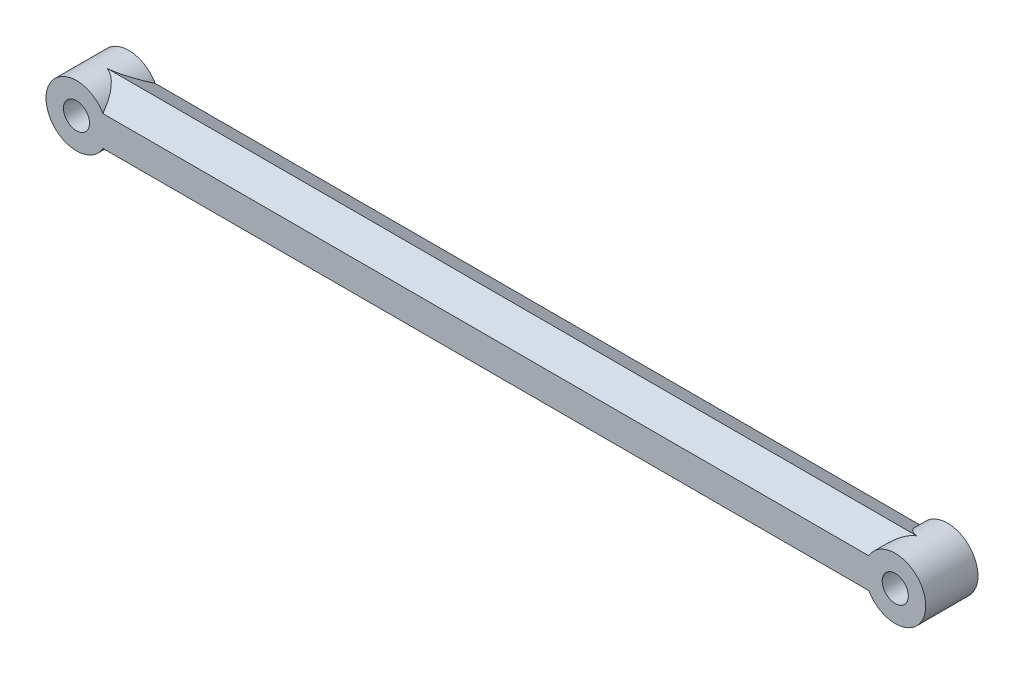
SolidWorks part; units mm, degrees
ref_plane "Front Plane" through (0, 0, 0) normal (0, 0, 1) x (1, 0, 0)
ref_plane "Top Plane" through (0, 0, 0) normal (0, 1, 0) x (1, 0, 0)
ref_plane "Right Plane" through (0, 0, 0) normal (1, 0, 0) x (0, 0, -1)
sketch "Sketch1" plane through (0, 0, 0) normal (0, 0, 1) x (1, 0, 0)
  line L0 (-47, 0) -> (47, 0) construction
  circle A0 centre (-47, 0) radius 1.5
  circle A1 centre (47, 0) radius 1.5
  circle A6 centre (-47, 0) radius 3.5
  circle A7 centre (47, 0) radius 3.5
  dimension "D2" = 3
  dimension "D3" = 7
  dimension "D1" = 94
extrude "Boss-Extrude1" add sketch "Sketch1" along normal mid plane 6
sketch "Sketch2" plane through (0, 0, 0) normal (1, 0, 0) x (0, 0, -1)
  line L0 (0, 0) -> (0, 3.4641) construction
  line L1 (-3, 1.7321) -> (-3, -1.7321)
  line L2 (-3, -1.7321) -> (0, -3.4641)
  line L3 (0, -3.4641) -> (3, -1.7321)
  line L4 (3, -1.7321) -> (3, 1.7321)
  line L5 (3, 1.7321) -> (0, 3.4641)
  line L6 (0, 3.4641) -> (-3, 1.7321)
  circle A0 centre (0, 0) radius 3 construction
  dimension "D1" = 6
extrude "Boss-Extrude2" add sketch "Sketch2" against normal up to surface and the other way up to surface up to face at (-43.5, 0, 3) other way up to face at (50.5, 0, 3)
